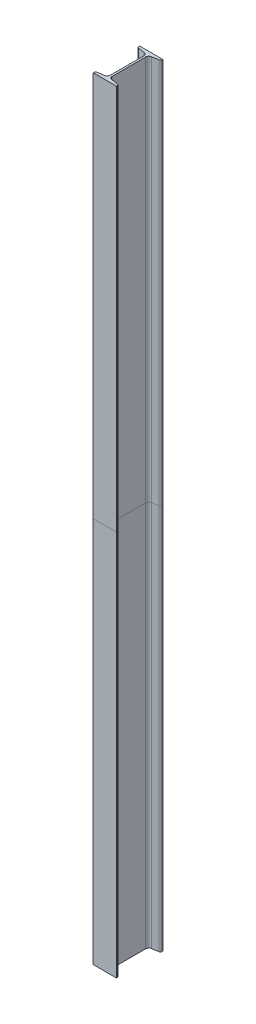
SolidWorks part; units mm, degrees
material "AISI 1020"
ref_plane "Front Plane" through (0, 0, 0) normal (0, 0, 1) x (1, 0, 0)
ref_plane "Top Plane" through (0, 0, 0) normal (0, 1, 0) x (1, 0, 0)
ref_plane "Right Plane" through (0, 0, 0) normal (1, 0, 0) x (0, 0, -1)
sketch "Sketch2" plane through (0, 0, 0) normal (0, 0, 1) x (1, 0, 0)
  line L0 (0, 0) -> (0, 2000)
  dimension "D1" = 2000
other "Sb beam 120 X 12(1)"
ref_plane "Plane1" through (0, 0, 0) normal (0, 1, 0) x (-1, 0, 0)
sketch "Sketch15" plane through (0, 0, 0) normal (0, 1, 0) x (-1, 0, 0)
  line L0 (-30, -60) -> (-30, -58.0801)
  line L1 (-26.6576, -54.1345) -> (-9.1847, -51.2221)
  line L2 (-2.5, -43.331) -> (-2.5, 43.331)
  line L3 (-9.1847, 51.2221) -> (-26.6576, 54.1345)
  line L4 (-30, 58.0801) -> (-30, 60)
  line L5 (-30, 60) -> (30, 60)
  line L6 (30, 60) -> (30, 58.0801)
  line L7 (26.6576, 54.1345) -> (9.1847, 51.2221)
  line L8 (2.5, 43.331) -> (2.5, -43.331)
  line L9 (9.1847, -51.2221) -> (26.6576, -54.1345)
  line L10 (30, -58.0801) -> (30, -60)
  line L11 (30, -60) -> (-30, -60)
  line L15 (-2.5, 0) -> (2.5, 0) construction
  arc A0 (-9.1847, -51.2221) -> (-2.5, -43.331) centre (-10.5, -43.331) ccw
  arc A1 (-2.5, 43.331) -> (-9.1847, 51.2221) centre (-10.5, 43.331) ccw
  arc A2 (9.1847, 51.2221) -> (2.5, 43.331) centre (10.5, 43.331) ccw
  arc A3 (2.5, -43.331) -> (9.1847, -51.2221) centre (10.5, -43.331) ccw
  arc A4 (-26.6576, 54.1345) -> (-30, 58.0801) centre (-26, 58.0801) cw
  arc A5 (26.6576, 54.1345) -> (30, 58.0801) centre (26, 58.0801) ccw
  arc A6 (-30, -58.0801) -> (-26.6576, -54.1345) centre (-26, -58.0801) cw
  arc A7 (30, -58.0801) -> (26.6576, -54.1345) centre (26, -58.0801) ccw
  point P1 (0, 60)
  point P8 (0, -60)
  point P21 (0, 0)
  point P34 (0, 0)
  dimension "RI" = 8
  dimension "D3" = 4
  dimension "BF" = 60
  dimension "D2" = 9.463
  dimension "DEPTH" = 120
  dimension "TW" = 5
  dimension "D1" = 86.662
sketch "Sketch16" plane through (0, 0, -60) normal (0, 0, -1) x (-1, 0, 0)
  line L0 (-30, 1000) -> (30, 1000)
  line L1 (-30, 2000) -> (-30, 0) construction
  line L2 (30, 2000) -> (30, 0) construction
  point P6 (0, 0)
split "Split1" trim tools "Sketch16" bodies to split 102 resulting bodies 103 104
ref_point "Point1"
